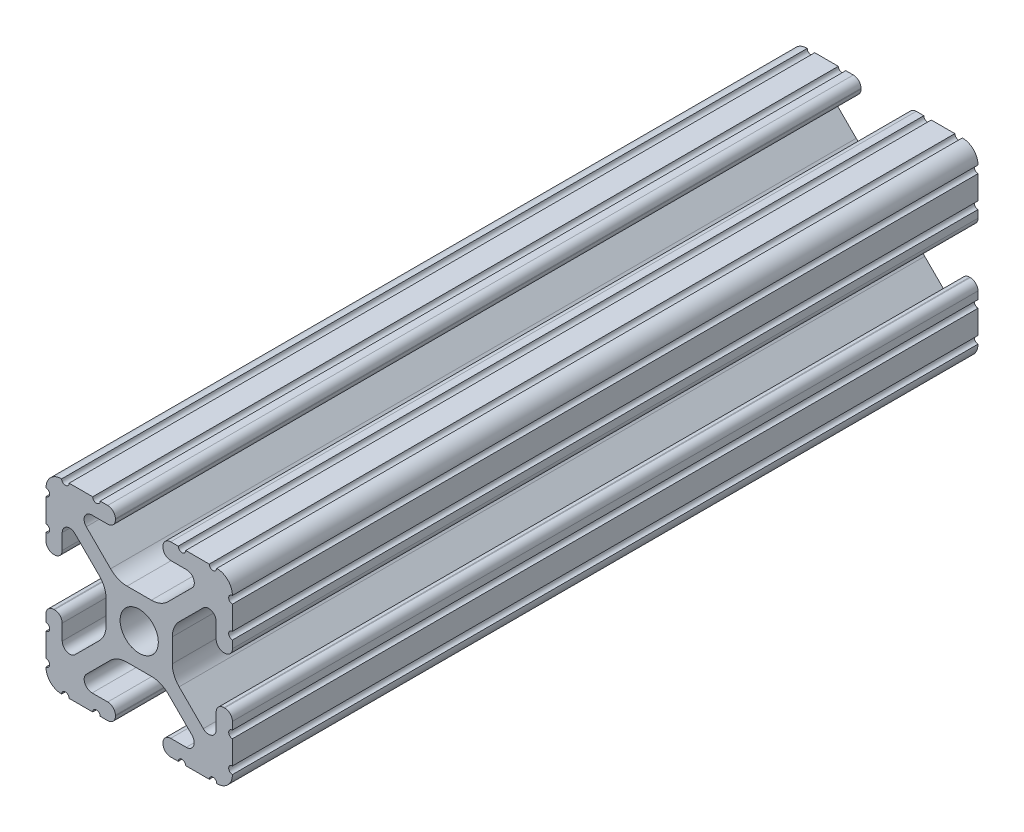
SolidWorks part; units mm, degrees
material "6061 Alloy"
ref_plane "Front Plane" through (0, 0, 0) normal (0, 0, 1) x (1, 0, 0)
ref_plane "Top Plane" through (0, 0, 0) normal (0, 1, 0) x (1, 0, 0)
ref_plane "Right Plane" through (0, 0, 0) normal (1, 0, 0) x (0, 0, -1)
sketch "Sketch1" plane through (0, 0, 0) normal (0, 0, 1) x (1, 0, 0)
  line L0 (-7.2072, 8.7245) -> (-3.9003, 5.4237)
  line L1 (-4.2875, 10.4902) -> (-6.4768, 10.4902)
  line L2 (-3.2384, 11.651) -> (-3.2384, 11.5392)
  line L3 (-5.3171, 12.7) -> (-4.2875, 12.7)
  line L4 (0, 13.4005) -> (0, -14.8534) construction
  line L5 (12.7, 0) -> (-13.9989, 0) construction
  line L6 (-9.5504, 12.7) -> (-6.3331, 12.7)
  line L7 (-12.7, 6.3331) -> (-12.7, 9.5504)
  line L8 (-12.7, 4.2875) -> (-12.7, 5.3171)
  line L9 (-11.5392, 3.2385) -> (-11.651, 3.2385)
  line L10 (-10.4902, 6.4021) -> (-10.4902, 4.2875)
  line L11 (-5.4405, 3.8388) -> (-8.737, 7.1292)
  line L12 (-4.5085, -1.5917) -> (-4.5085, 1.5917)
  line L13 (-1.7093, -4.4958) -> (1.7093, -4.4958)
  line L14 (3.9523, -5.4237) -> (7.1797, -8.6452)
  line L15 (6.4164, -10.4902) -> (4.2875, -10.4902)
  line L16 (3.2385, -11.5392) -> (3.2385, -11.651)
  line L17 (4.2875, -12.7) -> (5.3171, -12.7)
  line L18 (6.3331, -12.7) -> (9.5504, -12.7)
  line L19 (12.7, -9.5504) -> (12.7, -6.3331)
  line L20 (12.7, -5.3171) -> (12.7, -4.2875)
  line L21 (11.651, -3.2385) -> (11.5392, -3.2385)
  line L22 (10.4902, -4.2875) -> (10.4902, -6.4021)
  line L23 (8.737, -7.1292) -> (5.4405, -3.8388)
  line L24 (4.5085, -1.5917) -> (4.5085, 1.5917)
  line L25 (5.4405, 3.8388) -> (8.737, 7.1292)
  line L26 (10.4902, 6.4021) -> (10.4902, 4.2875)
  line L27 (11.5392, 3.2385) -> (11.651, 3.2385)
  line L28 (12.7, 4.2875) -> (12.7, 5.3171)
  line L29 (12.7, 6.3331) -> (12.7, 9.5504)
  line L30 (9.5504, 12.7) -> (6.3331, 12.7)
  line L31 (5.3171, 12.7) -> (4.2875, 12.7)
  line L32 (3.2384, 11.651) -> (3.2384, 11.5392)
  line L33 (4.2875, 10.4902) -> (6.4768, 10.4902)
  line L34 (7.2072, 8.7245) -> (3.9003, 5.4237)
  line L35 (1.6573, 4.4958) -> (-1.6573, 4.4958)
  line L36 (-8.737, -7.1292) -> (-5.4405, -3.8388)
  line L37 (-10.4902, -4.2875) -> (-10.4902, -6.4021)
  line L38 (-11.651, -3.2385) -> (-11.5392, -3.2385)
  line L39 (-12.7, -5.3171) -> (-12.7, -4.2875)
  line L40 (-12.7, -9.5504) -> (-12.7, -6.3331)
  line L41 (-6.3331, -12.7) -> (-9.5504, -12.7)
  line L42 (-4.2875, -12.7) -> (-5.3171, -12.7)
  line L43 (-3.2385, -11.5392) -> (-3.2385, -11.651)
  line L44 (-6.4164, -10.4902) -> (-4.2875, -10.4902)
  line L45 (-3.9523, -5.4237) -> (-7.1797, -8.6452)
  arc A0 (-7.2072, 8.7245) -> (-6.4768, 10.4902) centre (-6.4768, 9.4563) cw
  arc A1 (-3.2384, 11.5392) -> (-4.2875, 10.4902) centre (-4.2875, 11.5392) cw
  arc A2 (-4.2875, 12.7) -> (-3.2384, 11.651) centre (-4.2875, 11.651) cw
  arc A3 (-5.3171, 12.7) -> (-6.3331, 12.7) centre (-5.8251, 12.7) cw
  arc A4 (-9.5504, 12.7) -> (-10.5664, 12.6998) centre (-10.0584, 12.7) cw
  arc A5 (-12.6998, 10.5664) -> (-10.5664, 12.6998) centre (-10.5918, 10.5918) cw
  arc A6 (-12.6998, 10.5664) -> (-12.7, 9.5504) centre (-12.7, 10.0584) cw
  arc A7 (-12.7, 6.3331) -> (-12.7, 5.3171) centre (-12.7, 5.8251) cw
  arc A8 (-11.651, 3.2385) -> (-12.7, 4.2875) centre (-11.651, 4.2875) cw
  arc A9 (-10.4902, 4.2875) -> (-11.5392, 3.2385) centre (-11.5392, 4.2875) cw
  circle A10 centre (0, 0) radius 2.6035
  arc A11 (-10.4902, 6.4021) -> (-8.737, 7.1292) centre (-9.4628, 6.4021) cw
  arc A12 (-5.4405, 3.8388) -> (-4.5085, 1.5917) centre (-7.6835, 1.5917) cw
  arc A13 (-4.5085, -1.5917) -> (-5.4405, -3.8388) centre (-7.6835, -1.5917) cw
  arc A14 (-8.737, -7.1292) -> (-10.4902, -6.4021) centre (-9.4628, -6.4021) cw
  arc A15 (-1.7093, -4.4958) -> (-3.9523, -5.4237) centre (-1.7093, -7.6708) ccw
  arc A16 (3.9523, -5.4237) -> (1.7093, -4.4958) centre (1.7093, -7.6708) ccw
  arc A17 (6.4164, -10.4902) -> (7.1797, -8.6452) centre (6.4164, -9.4098) ccw
  arc A18 (4.2875, -10.4902) -> (3.2385, -11.5392) centre (4.2875, -11.5392) ccw
  arc A19 (3.2385, -11.651) -> (4.2875, -12.7) centre (4.2875, -11.651) ccw
  arc A20 (6.3331, -12.7) -> (5.3171, -12.7) centre (5.8251, -12.7) ccw
  arc A21 (10.5664, -12.6998) -> (9.5504, -12.7) centre (10.0584, -12.7) ccw
  arc A22 (10.5664, -12.6998) -> (12.6998, -10.5664) centre (10.5918, -10.5918) ccw
  arc A23 (12.7, -9.5504) -> (12.6998, -10.5664) centre (12.7, -10.0584) ccw
  arc A24 (12.7, -5.3171) -> (12.7, -6.3331) centre (12.7, -5.8251) ccw
  arc A25 (12.7, -4.2875) -> (11.651, -3.2385) centre (11.651, -4.2875) ccw
  arc A26 (11.5392, -3.2385) -> (10.4902, -4.2875) centre (11.5392, -4.2875) ccw
  arc A27 (8.737, -7.1292) -> (10.4902, -6.4021) centre (9.4628, -6.4021) ccw
  arc A28 (4.5085, -1.5917) -> (5.4405, -3.8388) centre (7.6835, -1.5917) ccw
  arc A29 (5.4405, 3.8388) -> (4.5085, 1.5917) centre (7.6835, 1.5917) ccw
  arc A30 (10.4902, 6.4021) -> (8.737, 7.1292) centre (9.4628, 6.4021) ccw
  arc A31 (10.4902, 4.2875) -> (11.5392, 3.2385) centre (11.5392, 4.2875) ccw
  arc A32 (11.651, 3.2385) -> (12.7, 4.2875) centre (11.651, 4.2875) ccw
  arc A33 (12.7, 6.3331) -> (12.7, 5.3171) centre (12.7, 5.8251) ccw
  arc A34 (12.6998, 10.5664) -> (12.7, 9.5504) centre (12.7, 10.0584) ccw
  arc A35 (12.6998, 10.5664) -> (10.5664, 12.6998) centre (10.5918, 10.5918) ccw
  arc A36 (9.5504, 12.7) -> (10.5664, 12.6998) centre (10.0584, 12.7) ccw
  arc A37 (5.3171, 12.7) -> (6.3331, 12.7) centre (5.8251, 12.7) ccw
  arc A38 (4.2875, 12.7) -> (3.2384, 11.651) centre (4.2875, 11.651) ccw
  arc A39 (3.2384, 11.5392) -> (4.2875, 10.4902) centre (4.2875, 11.5392) ccw
  arc A40 (7.2072, 8.7245) -> (6.4768, 10.4902) centre (6.4768, 9.4563) ccw
  arc A41 (1.6573, 4.4958) -> (3.9003, 5.4237) centre (1.6573, 7.6708) ccw
  arc A42 (-1.6573, 4.4958) -> (-3.9003, 5.4237) centre (-1.6573, 7.6708) cw
  arc A43 (-11.5392, -3.2385) -> (-10.4902, -4.2875) centre (-11.5392, -4.2875) cw
  arc A44 (-12.7, -4.2875) -> (-11.651, -3.2385) centre (-11.651, -4.2875) cw
  arc A45 (-12.7, -5.3171) -> (-12.7, -6.3331) centre (-12.7, -5.8251) cw
  arc A46 (-12.7, -9.5504) -> (-12.6998, -10.5664) centre (-12.7, -10.0584) cw
  arc A47 (-10.5664, -12.6998) -> (-12.6998, -10.5664) centre (-10.5918, -10.5918) cw
  arc A48 (-10.5664, -12.6998) -> (-9.5504, -12.7) centre (-10.0584, -12.7) cw
  arc A49 (-6.3331, -12.7) -> (-5.3171, -12.7) centre (-5.8251, -12.7) cw
  arc A50 (-3.2385, -11.651) -> (-4.2875, -12.7) centre (-4.2875, -11.651) cw
  arc A51 (-4.2875, -10.4902) -> (-3.2385, -11.5392) centre (-4.2875, -11.5392) cw
  arc A52 (-6.4164, -10.4902) -> (-7.1797, -8.6452) centre (-6.4164, -9.4098) cw
  dimension "D1" = 5.207
  dimension "D9" = 14.859
  dimension "D2" = 25.4
  dimension "D3" = 12.7
  dimension "D4" = 6.477
  dimension "D5" = 8.2042
  dimension "D6" = 9.017
  dimension "D8" = 2.2098
  dimension "D10" = 2.2098
extrude "Extrude1" add sketch "Sketch1" against normal blind 101.6
